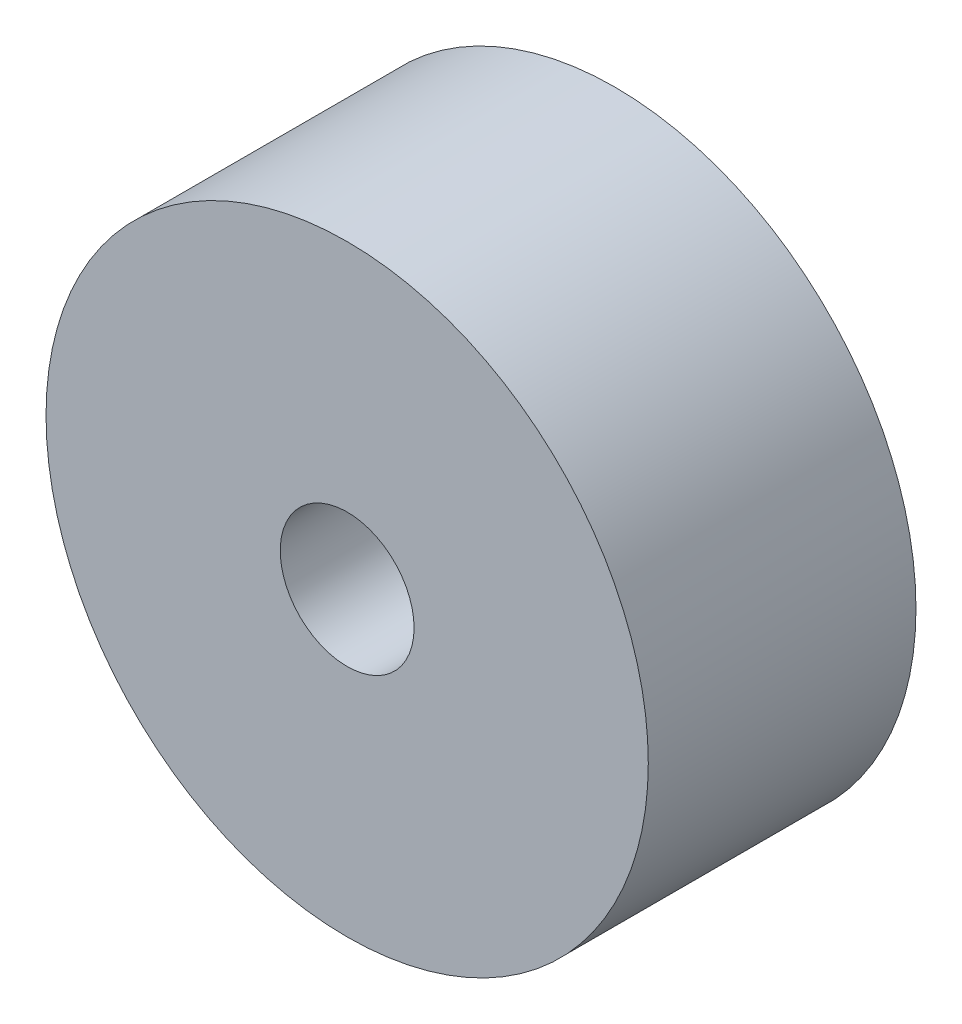
SolidWorks part; units mm, degrees
material "AISI 316 Annealed Stainless Steel Bar (SS)"
ref_plane "Front Plane" through (0, 0, 0) normal (0, 0, 1) x (1, 0, 0)
ref_plane "Top Plane" through (0, 0, 0) normal (0, 1, 0) x (1, 0, 0)
ref_plane "Right Plane" through (0, 0, 0) normal (1, 0, 0) x (0, 0, -1)
sketch "Sketch1" plane through (0, 0, 0) normal (0, 0, 1) x (1, 0, 0)
  circle A0 centre (0, 0) radius 5
  circle A1 centre (0, 0) radius 22.5
  dimension "D1" = 10
  dimension "D2" = 45
extrude "Boss-Extrude1" add sketch "Sketch1" along normal blind 20
